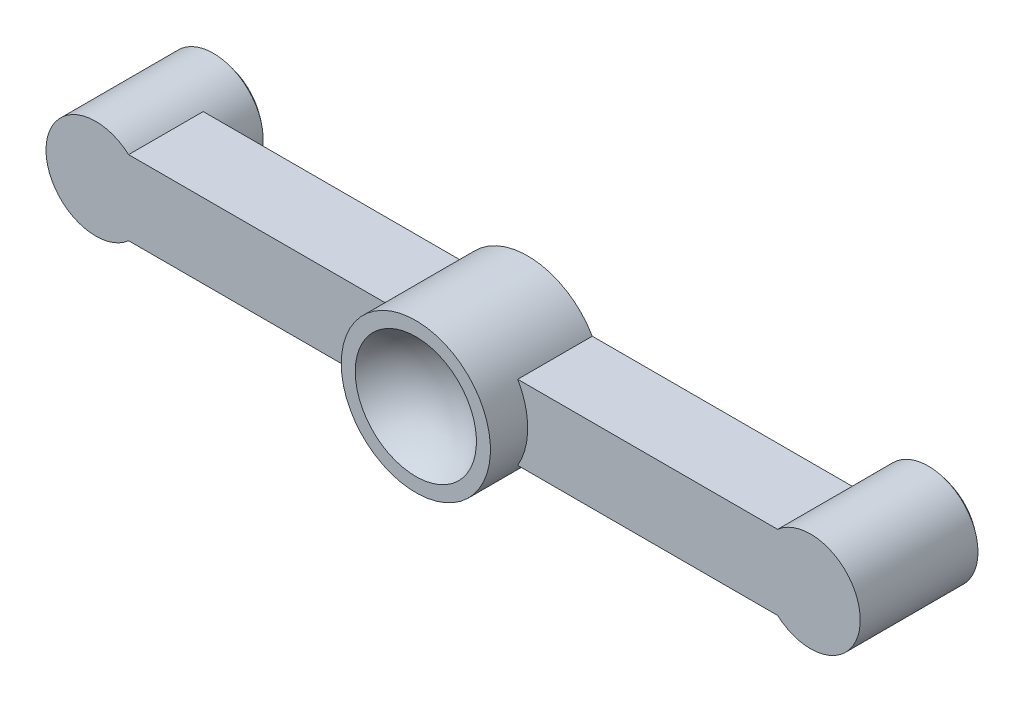
SolidWorks part; units mm, degrees
material "AISI 1045 钢，冷拔"
ref_plane "前视基准面" through (0, 0, 0) normal (0, 0, 1) x (1, 0, 0)
ref_plane "上视基准面" through (0, 0, 0) normal (0, 1, 0) x (1, 0, 0)
ref_plane "右视基准面" through (0, 0, 0) normal (1, 0, 0) x (0, 0, -1)
sketch "草图1" plane through (0, 0, 0) normal (0, 0, 1) x (1, 0, 0)
  line L1 (0, -6) -> (115, -6)
  line L2 (0, -6) -> (0, 6)
  line L3 (0, 6) -> (115, 6)
  line L4 (115, -6) -> (115, 6)
  circle A0 centre (115, 0) radius 8
  circle A1 centre (0, 0) radius 8
  circle A2 centre (57.5, 0) radius 12
  point P12 (57.5, -6)
  dimension "D3" = 16
  dimension "D4" = 16
  dimension "D5" = 24
  dimension "D1" = 115
  dimension "D2" = 12
extrude "凸台-拉伸1" add sketch "草图1" along normal blind 12 contours A1 | A0 | L1 L4 L3 L2 | A2
sketch "草图2" plane through (0, 0, 0) normal (0, 1, 0) x (1, 0, 0)
  line L0 (-8, 0) -> (-8, 6.9443)
  line L1 (0, 10) -> (0, 0)
  line L2 (-8, 0) -> (0, 0)
  line L3 (0, 10) -> (-10.12, 10)
  arc A0 (-8, 6.9443) -> (0, 10) centre (0, -2) cw
  dimension "D1" = 12
  dimension "D2" = 10
revolve "旋转2" add sketch "草图2" angle 360 about L1
ref_plane "基准面1" through (57.5, 0, 0) normal (1, 0, 0) x (0, 0, -1)
mirror "镜向1" about plane through (57.5, 0, 0) normal (1, 0, 0) of "旋转2"
sketch "草图3" plane through (0, 0, 0) normal (0, 1, 0) x (1, 0, 0)
  line L0 (57.5, -12) -> (57.5, -13)
  line L1 (57.5, -13) -> (54.5735, -13) construction
  line L2 (47.7532, -18) -> (45.5, -18)
  line L3 (45.5, -18) -> (45.5, -12)
  line L4 (45.5, -12) -> (57.5, -12)
  arc A1 (57.5, -13) -> (47.7532, -18) centre (57.5, -25) ccw
  dimension "D1" = 12
  dimension "D2" = 1
  dimension "D3" = 12
  dimension "D4" = 6
  dimension "D5" = 57.5
  dimension "D6" = 12
revolve "旋转3" add sketch "草图3" angle 360 about L0
